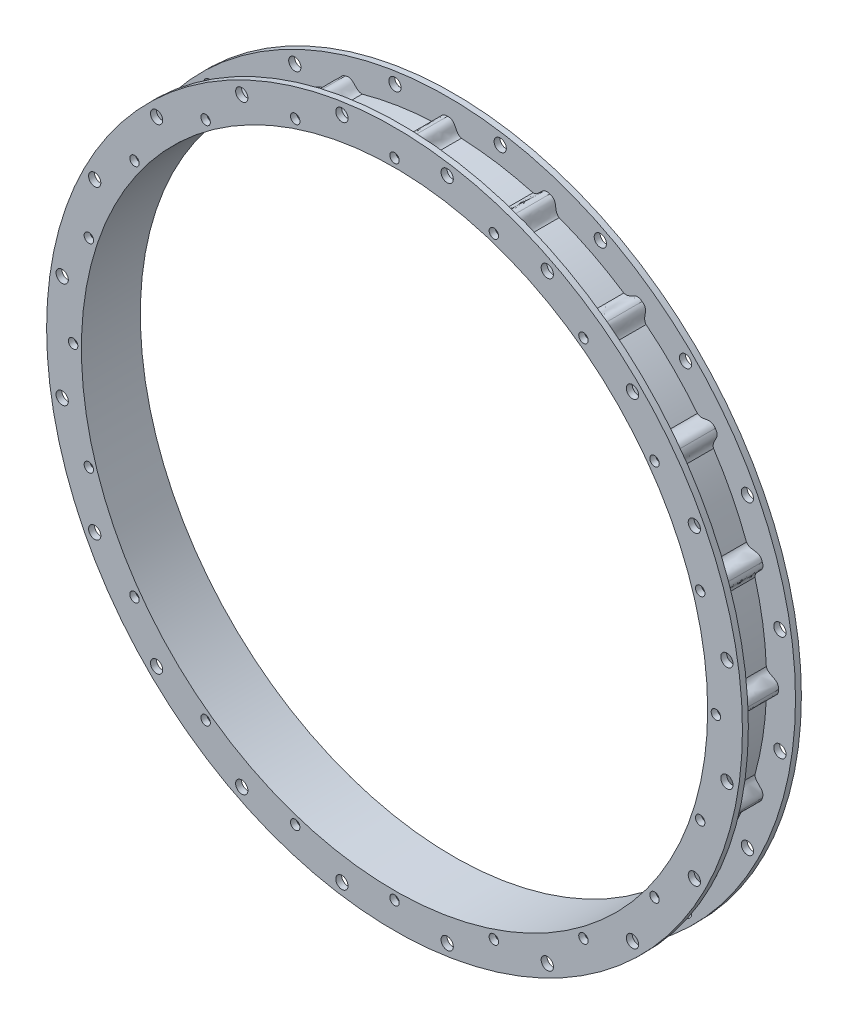
SolidWorks part; units mm, degrees
material "Maple"
ref_plane "Wasteboard" through (0, 0, 0) normal (0, 0, 1) x (1, 0, 0)
ref_plane "Left-Right" through (0, 0, 0) normal (0, 1, 0) x (1, 0, 0)
ref_plane "Front-Back" through (0, 0, 0) normal (1, 0, 0) x (0, 0, -1)
sketch "Sketch2" plane through (0, 0, 0) normal (0, 0, 1) x (1, 0, 0)
  circle A0 centre (0, 0) radius 192.0875 construction
  circle A1 centre (0, 0) radius 209.55 construction
  circle A2 centre (0, 0) radius 171.831 construction
  circle A3 centre (0, 0) radius 252.73 construction
  circle A4 centre (0, 0) radius 184.531 construction
  circle A5 centre (0, 0) radius 187.3885
  circle A6 centre (0, 0) radius 168.656
  dimension "D1" = 384.175
  dimension "D2" = 419.1
  dimension "D3" = 343.662
  dimension "D4" = 505.46
  dimension "D5" = 369.062
  dimension "D6" = 374.777
  dimension "D7" = 337.312
extrude "Boss-Extrude1" add sketch "Sketch2" along normal blind 3.175
sketch "Sketch3" plane through (0, 0, 3.175) normal (0, 0, 1) x (1, 0, 0)
  circle A0 centre (0, 0) radius 171.831
  circle A1 centre (0, 0) radius 168.656
  dimension "D1" = 343.662
extrude "Boss-Extrude2" add sketch "Sketch3" along normal blind 25.4
sketch "Sketch4" plane through (0, 0, 28.575) normal (0, 0, 1) x (1, 0, 0)
  circle A0 centre (0, 0) radius 187.3885
  circle A1 centre (0, 0) radius 168.656
extrude "Boss-Extrude3" add sketch "Sketch4" along normal blind 3.175
sketch "Sketch5" plane through (0, 0, 31.75) normal (0, 0, 1) x (1, 0, 0)
  line L0 (0, 0) -> (0, 196.8159) construction
  line L1 (-7.405, 171.6714) -> (7.405, 171.6714)
  line L2 (0, 178.2342) -> (22.1091, 178.2342) construction
  line L3 (50.9118, 162.6825) -> (45.3645, 143.4767) construction
  line L4 (46.0068, 165.5574) -> (60.092, 160.9809)
  line L5 (94.9151, 143.2376) -> (106.8967, 134.5325)
  line L6 (134.5325, 106.8967) -> (143.2376, 94.9151)
  line L7 (160.9809, 60.092) -> (165.5574, 46.0068)
  line L8 (171.6714, 7.405) -> (171.6714, -7.405)
  line L9 (165.5574, -46.0068) -> (160.9809, -60.092)
  line L10 (143.2376, -94.9151) -> (134.5325, -106.8967)
  line L11 (106.8967, -134.5325) -> (94.9151, -143.2376)
  line L12 (60.092, -160.9809) -> (46.0068, -165.5574)
  line L13 (7.405, -171.6714) -> (-7.405, -171.6714)
  line L14 (-46.0068, -165.5574) -> (-60.092, -160.9809)
  line L15 (-94.9151, -143.2376) -> (-106.8967, -134.5325)
  line L16 (-134.5325, -106.8967) -> (-143.2376, -94.9151)
  line L17 (-160.9809, -60.092) -> (-165.5574, -46.0068)
  line L18 (-171.6714, -7.405) -> (-171.6714, 7.405)
  line L19 (-165.5574, 46.0068) -> (-160.9809, 60.092)
  line L20 (-143.2376, 94.9151) -> (-134.5325, 106.8967)
  line L21 (-106.8967, 134.5325) -> (-94.9151, 143.2376)
  line L22 (-60.092, 160.9809) -> (-46.0068, 165.5574)
  circle A0 centre (0, 0) radius 171.831 construction
  circle A1 centre (0, 173.101) radius 1.27
  circle A3 centre (53.4912, 164.6288) radius 1.27
  circle A4 centre (101.7462, 140.0417) radius 1.27
  circle A5 centre (140.0417, 101.7462) radius 1.27
  circle A6 centre (164.6288, 53.4912) radius 1.27
  circle A7 centre (173.101, 0) radius 1.27
  circle A8 centre (164.6288, -53.4912) radius 1.27
  circle A9 centre (140.0417, -101.7462) radius 1.27
  circle A10 centre (101.7462, -140.0417) radius 1.27
  circle A11 centre (53.4912, -164.6288) radius 1.27
  circle A12 centre (0, -173.101) radius 1.27
  circle A13 centre (-53.4912, -164.6288) radius 1.27
  circle A14 centre (-101.7462, -140.0417) radius 1.27
  circle A15 centre (-140.0417, -101.7462) radius 1.27
  circle A16 centre (-164.6288, -53.4912) radius 1.27
  circle A17 centre (-173.101, 0) radius 1.27
  circle A18 centre (-164.6288, 53.4912) radius 1.27
  circle A19 centre (-140.0417, 101.7462) radius 1.27
  circle A20 centre (-101.7462, 140.0417) radius 1.27
  circle A21 centre (-53.4912, 164.6288) radius 1.27
  spline S0 degree 3 poles (0, 178.2342) (4.9619, 178.4345) (3.6283, 172.828) (7.405, 171.6714) knots 0 0 0 0 1 1 1 1
  spline S1 degree 3 poles (0, 178.2342) (-4.9619, 178.4345) (-3.6283, 172.828) (-7.405, 171.6714) knots 0 0 0 0 1 1 1 1
  spline S2 degree 3 poles (55.0774, 169.5108) (59.8584, 168.1679) (56.8575, 163.248) (60.092, 160.9809) knots 0 0 0 0 1 1 1 1
  spline S3 degree 3 poles (55.0774, 169.5108) (50.4202, 171.2346) (49.9561, 165.4904) (46.0068, 165.5574) knots 0 0 0 0 1 1 1 1
  spline S4 degree 3 poles (104.7634, 144.1945) (108.8954, 141.44) (104.5211, 137.6882) (106.8967, 134.5325) knots 0 0 0 0 1 1 1 1
  spline S5 degree 3 poles (104.7634, 144.1945) (100.8669, 147.2731) (98.6504, 141.9535) (94.9151, 143.2376) knots 0 0 0 0 1 1 1 1
  spline S6 degree 3 poles (144.1945, 104.7634) (147.2731, 100.8669) (141.9535, 98.6504) (143.2376, 94.9151) knots 0 0 0 0 1 1 1 1
  spline S7 degree 3 poles (144.1945, 104.7634) (141.44, 108.8954) (137.6882, 104.5211) (134.5325, 106.8967) knots 0 0 0 0 1 1 1 1
  spline S8 degree 3 poles (169.5108, 55.0774) (171.2346, 50.4202) (165.4904, 49.9561) (165.5574, 46.0068) knots 0 0 0 0 1 1 1 1
  spline S9 degree 3 poles (169.5108, 55.0774) (168.1679, 59.8584) (163.248, 56.8575) (160.9809, 60.092) knots 0 0 0 0 1 1 1 1
  spline S10 degree 3 poles (178.2342, 0) (178.4345, -4.9619) (172.828, -3.6283) (171.6714, -7.405) knots 0 0 0 0 1 1 1 1
  spline S11 degree 3 poles (178.2342, 0) (178.4345, 4.9619) (172.828, 3.6283) (171.6714, 7.405) knots 0 0 0 0 1 1 1 1
  spline S12 degree 3 poles (169.5108, -55.0774) (168.1679, -59.8584) (163.248, -56.8575) (160.9809, -60.092) knots 0 0 0 0 1 1 1 1
  spline S13 degree 3 poles (169.5108, -55.0774) (171.2346, -50.4202) (165.4904, -49.9561) (165.5574, -46.0068) knots 0 0 0 0 1 1 1 1
  spline S14 degree 3 poles (144.1945, -104.7634) (141.44, -108.8954) (137.6882, -104.5211) (134.5325, -106.8967) knots 0 0 0 0 1 1 1 1
  spline S15 degree 3 poles (144.1945, -104.7634) (147.2731, -100.8669) (141.9535, -98.6504) (143.2376, -94.9151) knots 0 0 0 0 1 1 1 1
  spline S16 degree 3 poles (104.7634, -144.1945) (100.8669, -147.2731) (98.6504, -141.9535) (94.9151, -143.2376) knots 0 0 0 0 1 1 1 1
  spline S17 degree 3 poles (104.7634, -144.1945) (108.8954, -141.44) (104.5211, -137.6882) (106.8967, -134.5325) knots 0 0 0 0 1 1 1 1
  spline S18 degree 3 poles (55.0774, -169.5108) (50.4202, -171.2346) (49.9561, -165.4904) (46.0068, -165.5574) knots 0 0 0 0 1 1 1 1
  spline S19 degree 3 poles (55.0774, -169.5108) (59.8584, -168.1679) (56.8575, -163.248) (60.092, -160.9809) knots 0 0 0 0 1 1 1 1
  spline S20 degree 3 poles (0, -178.2342) (-4.9619, -178.4345) (-3.6283, -172.828) (-7.405, -171.6714) knots 0 0 0 0 1 1 1 1
  spline S21 degree 3 poles (0, -178.2342) (4.9619, -178.4345) (3.6283, -172.828) (7.405, -171.6714) knots 0 0 0 0 1 1 1 1
  spline S22 degree 3 poles (-55.0774, -169.5108) (-59.8584, -168.1679) (-56.8575, -163.248) (-60.092, -160.9809) knots 0 0 0 0 1 1 1 1
  spline S23 degree 3 poles (-55.0774, -169.5108) (-50.4202, -171.2346) (-49.9561, -165.4904) (-46.0068, -165.5574) knots 0 0 0 0 1 1 1 1
  spline S24 degree 3 poles (-104.7634, -144.1945) (-108.8954, -141.44) (-104.5211, -137.6882) (-106.8967, -134.5325) knots 0 0 0 0 1 1 1 1
  spline S25 degree 3 poles (-104.7634, -144.1945) (-100.8669, -147.2731) (-98.6504, -141.9535) (-94.9151, -143.2376) knots 0 0 0 0 1 1 1 1
  spline S26 degree 3 poles (-144.1945, -104.7634) (-147.2731, -100.8669) (-141.9535, -98.6504) (-143.2376, -94.9151) knots 0 0 0 0 1 1 1 1
  spline S27 degree 3 poles (-144.1945, -104.7634) (-141.44, -108.8954) (-137.6882, -104.5211) (-134.5325, -106.8967) knots 0 0 0 0 1 1 1 1
  spline S28 degree 3 poles (-169.5108, -55.0774) (-171.2346, -50.4202) (-165.4904, -49.9561) (-165.5574, -46.0068) knots 0 0 0 0 1 1 1 1
  spline S29 degree 3 poles (-169.5108, -55.0774) (-168.1679, -59.8584) (-163.248, -56.8575) (-160.9809, -60.092) knots 0 0 0 0 1 1 1 1
  spline S30 degree 3 poles (-178.2342, 0) (-178.4345, 4.9619) (-172.828, 3.6283) (-171.6714, 7.405) knots 0 0 0 0 1 1 1 1
  spline S31 degree 3 poles (-178.2342, 0) (-178.4345, -4.9619) (-172.828, -3.6283) (-171.6714, -7.405) knots 0 0 0 0 1 1 1 1
  spline S32 degree 3 poles (-169.5108, 55.0774) (-168.1679, 59.8584) (-163.248, 56.8575) (-160.9809, 60.092) knots 0 0 0 0 1 1 1 1
  spline S33 degree 3 poles (-169.5108, 55.0774) (-171.2346, 50.4202) (-165.4904, 49.9561) (-165.5574, 46.0068) knots 0 0 0 0 1 1 1 1
  spline S34 degree 3 poles (-144.1945, 104.7634) (-141.44, 108.8954) (-137.6882, 104.5211) (-134.5325, 106.8967) knots 0 0 0 0 1 1 1 1
  spline S35 degree 3 poles (-144.1945, 104.7634) (-147.2731, 100.8669) (-141.9535, 98.6504) (-143.2376, 94.9151) knots 0 0 0 0 1 1 1 1
  spline S36 degree 3 poles (-104.7634, 144.1945) (-100.8669, 147.2731) (-98.6504, 141.9535) (-94.9151, 143.2376) knots 0 0 0 0 1 1 1 1
  spline S37 degree 3 poles (-104.7634, 144.1945) (-108.8954, 141.44) (-104.5211, 137.6882) (-106.8967, 134.5325) knots 0 0 0 0 1 1 1 1
  spline S38 degree 3 poles (-55.0774, 169.5108) (-50.4202, 171.2346) (-49.9561, 165.4904) (-46.0068, 165.5574) knots 0 0 0 0 1 1 1 1
  spline S39 degree 3 poles (-55.0774, 169.5108) (-59.8584, 168.1679) (-56.8575, 163.248) (-60.092, 160.9809) knots 0 0 0 0 1 1 1 1
  point P191 (0, 0)
  dimension "D1" = 2.54
  dimension "D2" = 20
extrude "Boss-Extrude4" add sketch "Sketch5" against normal blind 30.48
sketch "Sketch6" plane through (0, 0, 31.75) normal (0, 0, 1) x (1, 0, 0)
  line L0 (0, 0) -> (0, 196.8159) construction
  circle A1 centre (0, 173.101) radius 2.54
  circle A2 centre (53.4912, 164.6288) radius 2.54
  circle A22 centre (101.7462, 140.0417) radius 2.54
  circle A23 centre (140.0417, 101.7462) radius 2.54
  circle A24 centre (164.6288, 53.4912) radius 2.54
  circle A25 centre (173.101, 0) radius 2.54
  circle A26 centre (164.6288, -53.4912) radius 2.54
  circle A27 centre (140.0417, -101.7462) radius 2.54
  circle A28 centre (101.7462, -140.0417) radius 2.54
  circle A29 centre (53.4912, -164.6288) radius 2.54
  circle A30 centre (0, -173.101) radius 2.54
  circle A31 centre (-53.4912, -164.6288) radius 2.54
  circle A32 centre (-101.7462, -140.0417) radius 2.54
  circle A33 centre (-140.0417, -101.7462) radius 2.54
  circle A34 centre (-164.6288, -53.4912) radius 2.54
  circle A35 centre (-173.101, 0) radius 2.54
  circle A36 centre (-164.6288, 53.4912) radius 2.54
  circle A37 centre (-140.0417, 101.7462) radius 2.54
  circle A38 centre (-101.7462, 140.0417) radius 2.54
  circle A39 centre (-53.4912, 164.6288) radius 2.54
  point P45 (0, 0)
  point P191 (0, 0)
  dimension "D1" = 5.08
  dimension "D2" = 20
extrude "Cut-Extrude3" cut sketch "Sketch6" against normal blind 3.175
sketch "Sketch7" plane through (0, 0, 31.75) normal (0, 0, 1) x (1, 0, 0)
  line L0 (0, 0) -> (0, 203.459) construction
  circle A0 centre (28.3505, 178.9978) radius 3.302
  circle A2 centre (82.2762, 161.4762) radius 3.302
  circle A3 centre (128.1483, 128.1483) radius 3.302
  circle A4 centre (161.4762, 82.2762) radius 3.302
  circle A5 centre (178.9978, 28.3505) radius 3.302
  circle A6 centre (178.9978, -28.3505) radius 3.302
  circle A7 centre (161.4762, -82.2762) radius 3.302
  circle A8 centre (128.1483, -128.1483) radius 3.302
  circle A9 centre (82.2762, -161.4762) radius 3.302
  circle A10 centre (28.3505, -178.9978) radius 3.302
  circle A11 centre (-28.3505, -178.9978) radius 3.302
  circle A12 centre (-82.2762, -161.4762) radius 3.302
  circle A13 centre (-128.1483, -128.1483) radius 3.302
  circle A14 centre (-161.4762, -82.2762) radius 3.302
  circle A15 centre (-178.9978, -28.3505) radius 3.302
  circle A16 centre (-178.9978, 28.3505) radius 3.302
  circle A17 centre (-161.4762, 82.2762) radius 3.302
  circle A18 centre (-128.1483, 128.1483) radius 3.302
  circle A19 centre (-82.2762, 161.4762) radius 3.302
  circle A20 centre (-28.3505, 178.9978) radius 3.302
  point P45 (0, 0)
  dimension "D1" = 6.604
  dimension "D2" = 20
extrude "Cut-Extrude4" cut sketch "Sketch7" against normal through all
